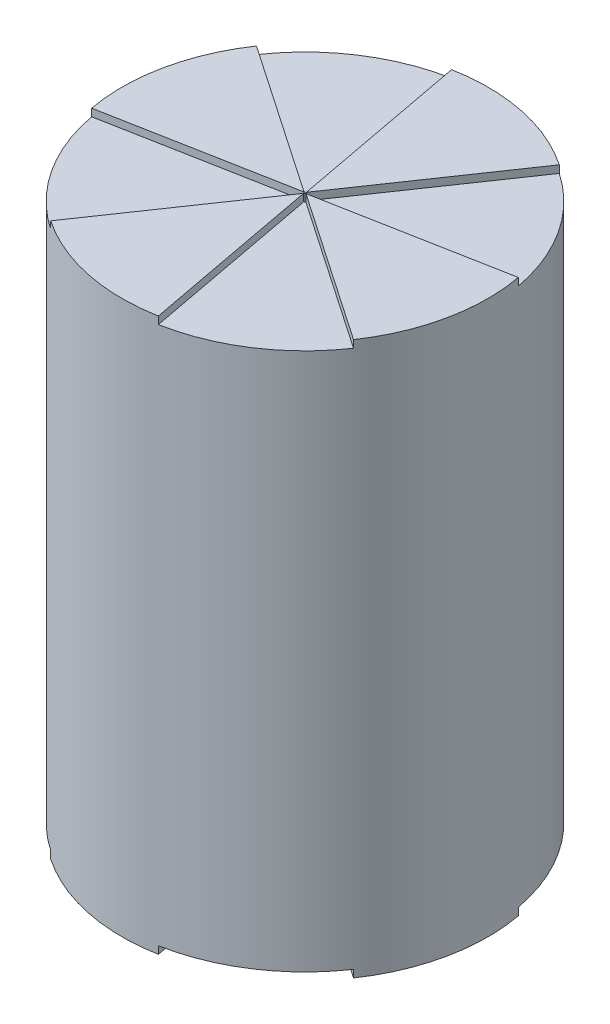
SolidWorks part; units mm, degrees
material "Nylon 101"
ref_plane "Front" through (0, 0, 0) normal (0, 0, 1) x (1, 0, 0)
ref_plane "Top" through (0, 0, 0) normal (0, 1, 0) x (1, 0, 0)
ref_plane "Right" through (0, 0, 0) normal (1, 0, 0) x (0, 0, -1)
sketch "Sketch1" plane through (0, 0, 0) normal (0, 1, 0) x (1, 0, 0)
  circle A0 centre (0, 0) radius 62.23
  dimension "D1" = 124.46
extrude "Boss-Extrude1" add sketch "Sketch1" along normal blind 187.96
sketch "Sketch2" plane through (0, 187.96, 0) normal (0, 1, 0) x (1, 0, 0)
  line L6 (-34.9778, -51.4697) -> (0.0216, -0.2531)
  line L7 (-0.2231, 0.1215) -> (-61.187, -11.3458)
  arc A6 (-34.9778, -51.4697) -> (-61.187, -11.3458) centre (0, 0) cw
  arc A7 (0.0216, -0.2531) -> (-0.2231, 0.1215) centre (0, 0) cw
  circle A8 centre (0, 0) radius 62.23 construction
  dimension "D1" = 45
  dimension "D3" = 62.033
  dimension "D2" = 0.254
extrude "Cut-Extrude7" cut sketch "Sketch2" against normal blind 2.54
pattern_circular "CirPattern2" count 4 over 360 about axis through (0, 0, 0) along (0, 1, 0) of "Cut-Extrude7"
ref_plane "Plane1" through (0, 93.98, 0) normal (0, 1, 0) x (1, 0, 0)
mirror "Mirror1" about plane through (0, 93.98, 0) normal (0, 1, 0) of "CirPattern2", "Cut-Extrude7"
